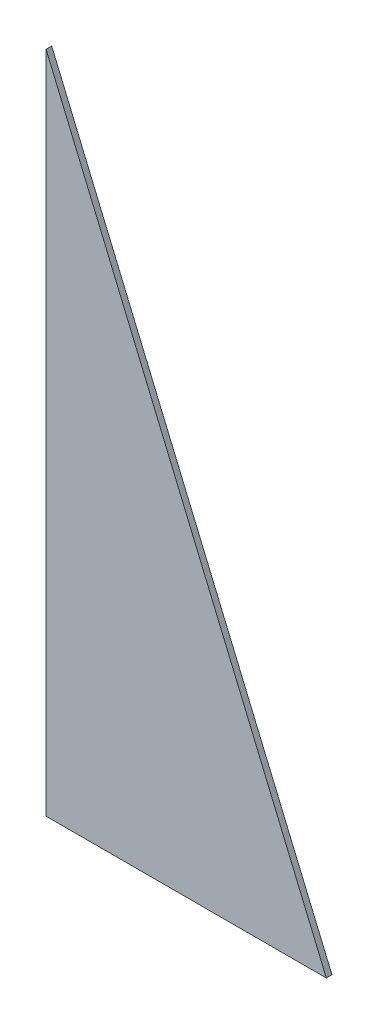
SolidWorks part; units mm, degrees
material "1.0037 (S235JR)"
ref_plane "Front Plane" through (0, 0, 0) normal (0, 0, 1) x (1, 0, 0)
ref_plane "Top Plane" through (0, 0, 0) normal (0, 1, 0) x (1, 0, 0)
ref_plane "Right Plane" through (0, 0, 0) normal (1, 0, 0) x (0, 0, -1)
sketch "Sketch1" plane through (0, 0, 0) normal (0, 0, 1) x (1, 0, 0)
  line L1 (-50, 118.5) -> (50, 118.5)
  line L2 (-50, 118.5) -> (-50, -118.5)
  line L3 (-50, -118.5) -> (50, -118.5)
  line L4 (50, 118.5) -> (50, -118.5)
  line L5 (-50, 118.5) -> (50, -118.5) construction
  line L6 (-50, -118.5) -> (50, 118.5) construction
  point P0 (0, 0)
  dimension "D1" = 237
  dimension "D2" = 100
extrude "Boss-Extrude1" add sketch "Sketch1" along normal blind 2
sketch "Sketch2" plane through (0, 0, 2) normal (0, 0, 1) x (1, 0, 0)
  line L0 (-50, 118.5) -> (50, -118.5)
  line L1 (50, -118.5) -> (87.0015, 120.9547)
  line L2 (87.0015, 120.9547) -> (-50, 118.5)
extrude "Cut-Extrude1" cut sketch "Sketch2" against normal through all
